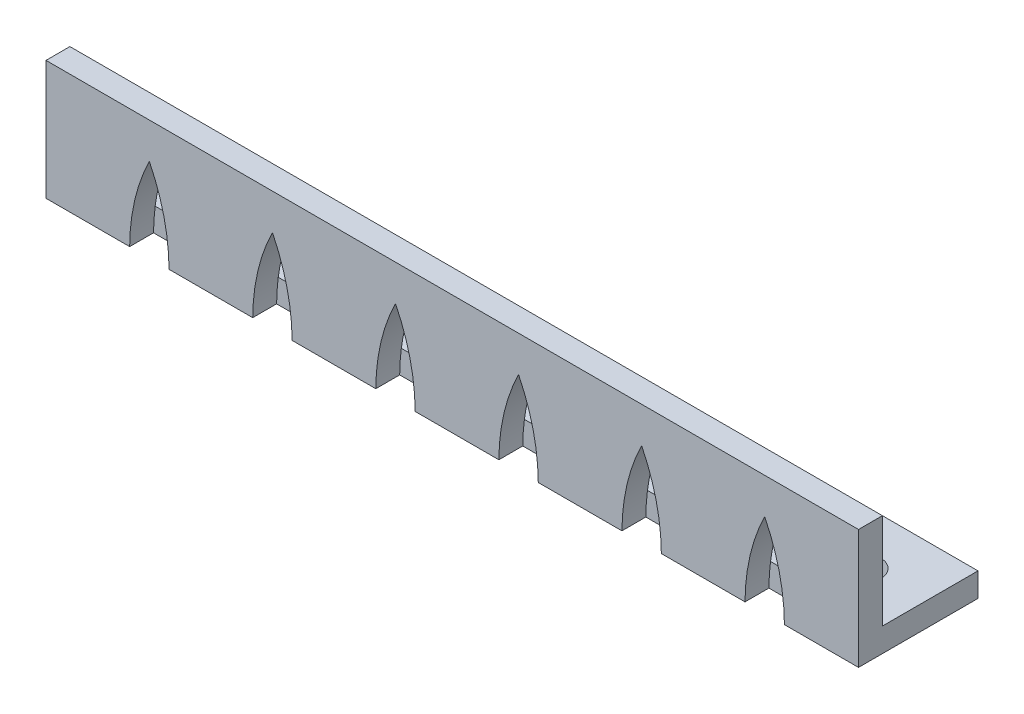
SolidWorks part; units mm, degrees
material "ABS"
ref_plane "Front Plane" through (0, 0, 0) normal (0, 0, 1) x (1, 0, 0)
ref_plane "Top Plane" through (0, 0, 0) normal (0, 1, 0) x (1, 0, 0)
ref_plane "Right Plane" through (0, 0, 0) normal (1, 0, 0) x (0, 0, -1)
ref_plane "Front Plane1" through (0, 0, 5) normal (0, 0, 1) x (1, 0, 0)
sketch "Sketch1" plane through (0, 0, 0) normal (0, 1, 0) x (1, 0, 0)
  line L0 (-34, 5) -> (34, -5) construction
  line L1 (-34, 5) -> (34, 5)
  line L2 (-34, 5) -> (-34, -5)
  line L3 (-34, -5) -> (34, -5)
  line L4 (34, 5) -> (34, -5)
  circle A0 centre (-31, 0.35) radius 1.5025
  circle A1 centre (-21, 0.35) radius 1.5025
  circle A2 centre (-11, 0.35) radius 1.5025
  circle A3 centre (-1, 0.35) radius 1.5025
  circle A4 centre (9, 0.35) radius 1.5025
  circle A5 centre (19, 0.35) radius 1.5025
  circle A6 centre (29, 0.35) radius 1.5025
  dimension "D3" = 3.005
  dimension "D4" = 3
  dimension "D5" = 5.35
  dimension "D8" = 5.35
  dimension "D1" = 68
  dimension "D2" = 10
  dimension "D7" = 5
  dimension "D6" = 7
extrude "Boss-Extrude1" add sketch "Sketch1" along normal blind 10
sketch "Sketch2" plane through (0, 0, 0) normal (0, 0, 1) x (1, 0, 0)
  line L0 (34, 10) -> (34, 0) construction
  line L1 (-34, 10) -> (34, 10)
  line L2 (-34, 10) -> (-34, 2)
  line L3 (-34, 2) -> (34, 2)
  line L4 (34, 10) -> (34, 2)
  dimension "D1" = 8
extrude "Cut-Extrude1" cut sketch "Sketch2" against normal up to next and the other way blind 3
sketch "Sketch3" plane through (0, 0, 5) normal (0, 0, 1) x (1, 0, 0)
  line L0 (-34, 0) -> (34, 0) construction
  line L1 (-27, 10) -> (-27, 0) construction
  line L2 (-34, 10) -> (34, 10) construction
  line L3 (-34, 10) -> (-34, 0) construction
  line L4 (-25.35, 10) -> (-25.35, 0) construction
  line L5 (-23.7, 10) -> (-23.7, 0) construction
  line L6 (-26.175, 10) -> (-26.175, 0) construction
  line L7 (-24.525, 10) -> (-24.525, 0) construction
  line L8 (-26.175, 5) -> (-24.525, 5) construction
  line L9 (-27, 0) -> (-23.7, 0)
  line L10 (-16.7, 0) -> (-13.4, 0)
  line L11 (-6.4, 0) -> (-3.1, 0)
  line L12 (3.9, 0) -> (7.2, 0)
  line L13 (14.2, 0) -> (17.5, 0)
  line L14 (24.5, 0) -> (27.8, 0)
  spline S0 degree 2 poles (-25.35, 7) (-26.9651, 3.725) (-27, 0) knots 0 0 0 1 1 1
  spline S1 degree 2 poles (-25.35, 7) (-23.7349, 3.725) (-23.7, 0) knots 0 0 0 1 1 1
  spline S2 degree 2 poles (-15.05, 7) (-13.4349, 3.725) (-13.4, 0) knots 0 0 0 1 1 1
  spline S3 degree 2 poles (-15.05, 7) (-16.6651, 3.725) (-16.7, 0) knots 0 0 0 1 1 1
  spline S4 degree 2 poles (-4.75, 7) (-3.1349, 3.725) (-3.1, 0) knots 0 0 0 1 1 1
  spline S5 degree 2 poles (-4.75, 7) (-6.3651, 3.725) (-6.4, 0) knots 0 0 0 1 1 1
  spline S6 degree 2 poles (5.55, 7) (7.1651, 3.725) (7.2, 0) knots 0 0 0 1 1 1
  spline S7 degree 2 poles (5.55, 7) (3.9349, 3.725) (3.9, 0) knots 0 0 0 1 1 1
  spline S8 degree 2 poles (15.85, 7) (17.4651, 3.725) (17.5, 0) knots 0 0 0 1 1 1
  spline S9 degree 2 poles (15.85, 7) (14.2349, 3.725) (14.2, 0) knots 0 0 0 1 1 1
  spline S10 degree 2 poles (26.15, 7) (27.7651, 3.725) (27.8, 0) knots 0 0 0 1 1 1
  spline S11 degree 2 poles (26.15, 7) (24.5349, 3.725) (24.5, 0) knots 0 0 0 1 1 1
  point P0 (-25.35, 7)
  dimension "D1" = 7
  dimension "D2" = 7
  dimension "D3" = 1.65
  dimension "D4" = 1.65
  dimension "D5" = 0.825
  dimension "D6" = 0.825
  dimension "D7" = 5
  dimension "D8" = 6
extrude "Cut-Extrude2" cut sketch "Sketch3" against normal blind 2
